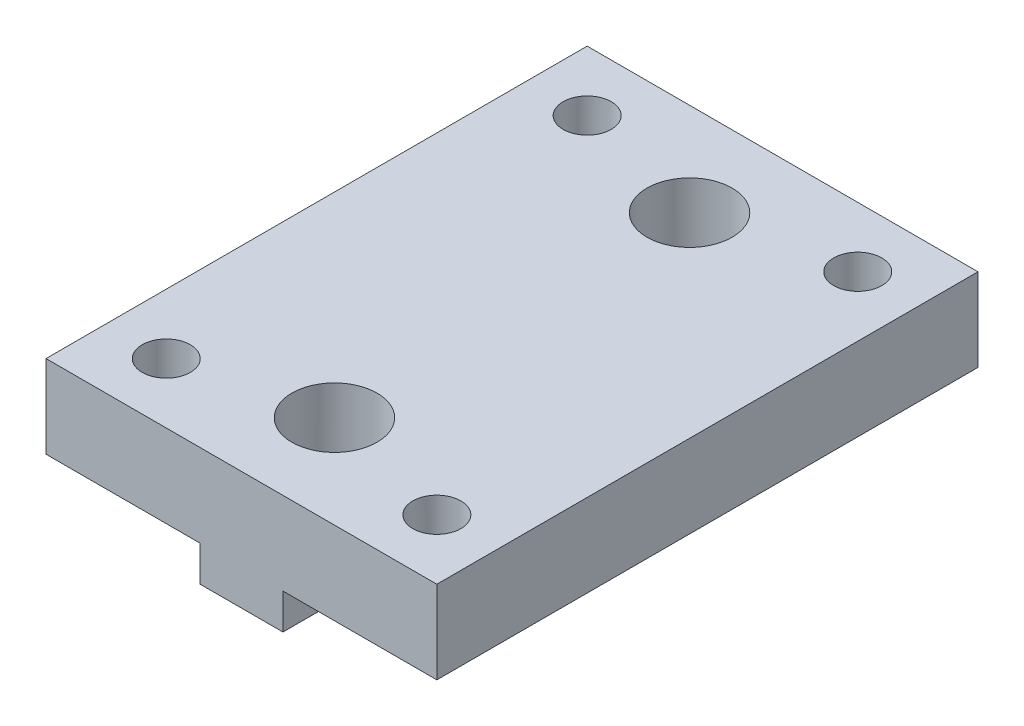
SolidWorks part; units mm, degrees
ref_plane "Front Plane" through (0, 0, 0) normal (0, 0, 1) x (1, 0, 0)
ref_plane "Top Plane" through (0, 0, 0) normal (0, 1, 0) x (1, 0, 0)
ref_plane "Right Plane" through (0, 0, 0) normal (1, 0, 0) x (0, 0, -1)
sketch "Sketch1" plane through (0, 0, 0) normal (0, 1, 0) x (1, 0, 0)
  line L1 (-16.51, 22.86) -> (16.51, 22.86)
  line L2 (-16.51, 22.86) -> (-16.51, -22.86)
  line L3 (-16.51, -22.86) -> (16.51, -22.86)
  line L4 (16.51, 22.86) -> (16.51, -22.86)
  circle A0 centre (-11.43, 17.78) radius 2.032
  circle A1 centre (11.43, 17.78) radius 2.032
  circle A2 centre (-11.43, -17.78) radius 2.032
  circle A3 centre (11.43, -17.78) radius 2.032
  dimension "D5" = 4.064
  dimension "D6" = 5.08
  dimension "D7" = 5.08
  dimension "D8" = 4.064
  dimension "D9" = 5.08
  dimension "D10" = 5.08
  dimension "D11" = 4.064
  dimension "D12" = 5.08
  dimension "D14" = 4.064
  dimension "D15" = 5.08
  dimension "D16" = 5.08
  dimension "D1" = 33.02
  dimension "D2" = 45.72
  dimension "D3" = 16.51
  dimension "D4" = 22.86
  dimension "D13" = 5.08
extrude "Boss-Extrude1" add sketch "Sketch1" along normal blind 10
sketch "Sketch2" plane through (0, 10, 0) normal (0, 1, 0) x (1, 0, 0)
  circle A1 centre (0, 15) radius 3.6
  circle A2 centre (0, -15) radius 3.6
  dimension "D1" = 7.2
  dimension "D2" = 7.2
  dimension "D4" = 15
  dimension "D3" = 30
extrude "Cut-Extrude1" cut sketch "Sketch2" against normal blind 10
sketch "Sketch4" plane through (0, 0, 0) normal (0, -1, 0) x (1, 0, 0)
  line L0 (-16.51, 22.86) -> (16.51, 22.86) construction
  line L1 (16.51, -22.86) -> (3.51, -22.86)
  line L2 (16.51, -22.86) -> (16.51, 22.86)
  line L3 (16.51, 22.86) -> (3.51, 22.86)
  line L4 (3.51, -22.86) -> (3.51, 22.86)
  line L6 (-16.51, -22.86) -> (-3.51, -22.86)
  line L7 (-16.51, -22.86) -> (-16.51, 22.86)
  line L8 (-16.51, 22.86) -> (-3.51, 22.86)
  line L9 (-3.51, -22.86) -> (-3.51, 22.86)
  dimension "D1" = 13
  dimension "D2" = 13
extrude "Cut-Extrude4" cut sketch "Sketch4" against normal blind 3
